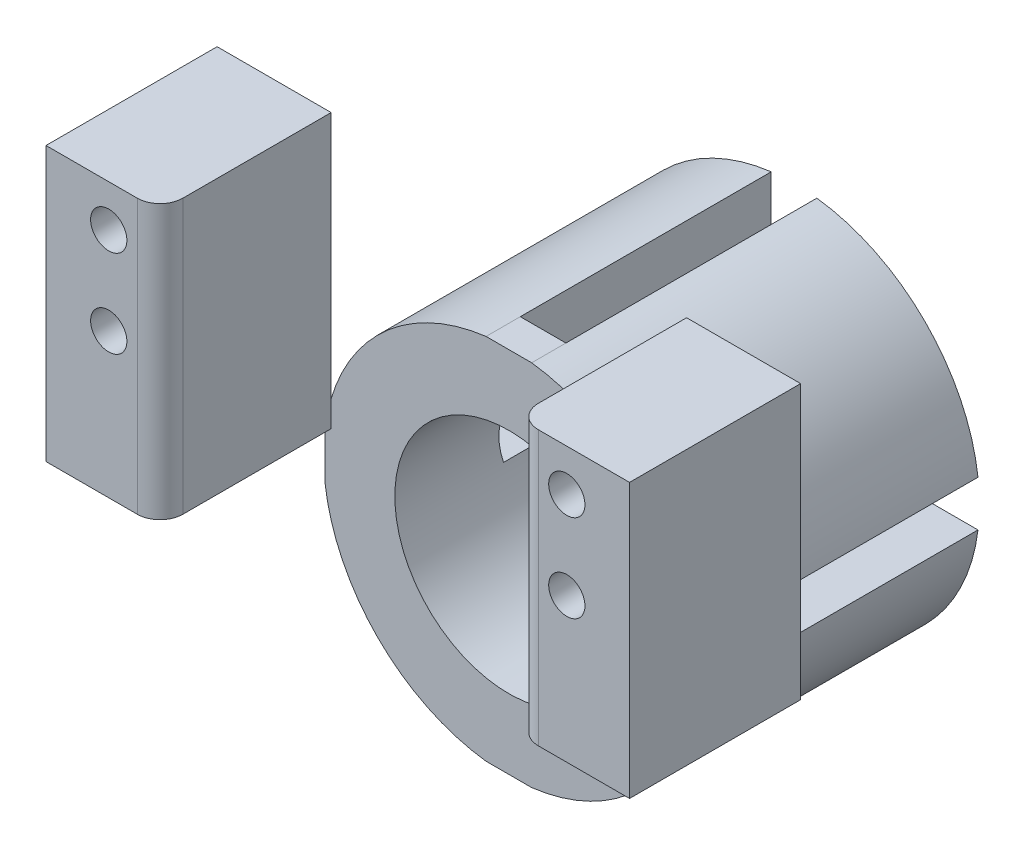
SolidWorks part; units mm, degrees
ref_plane "Front Plane" through (0, 0, 0) normal (0, 0, 1) x (1, 0, 0)
ref_plane "Top Plane" through (0, 0, 0) normal (0, 1, 0) x (1, 0, 0)
ref_plane "Right Plane" through (0, 0, 0) normal (1, 0, 0) x (0, 0, -1)
sketch "Sketch2" plane through (0, 0, 0) normal (0, 0, 1) x (1, 0, 0)
  circle A0 centre (0, 0) radius 38.1
  circle A1 centre (0, 0) radius 34.925
  dimension "D1" = 76.2
  dimension "D2" = 69.85
sketch "Sketch4" plane through (0, 0, 0) normal (0, 0, 1) x (1, 0, 0)
  line L0 (-16.6687, -2.54) -> (-16.6687, 2.54) construction
  line L1 (-12.7, 0) -> (-20.6375, 0) construction
  line L2 (-12.4434, 2.54) -> (-20.4806, 2.54)
  line L3 (-12.4434, -2.54) -> (-20.4806, -2.54)
  line L4 (-2.54, 12.4434) -> (-2.54, 20.4806)
  line L5 (2.54, 12.4434) -> (2.54, 20.4806)
  line L6 (12.4434, 2.54) -> (20.4806, 2.54)
  line L7 (12.4434, -2.54) -> (20.4806, -2.54)
  line L8 (2.54, -12.4434) -> (2.54, -20.4806)
  line L9 (-2.54, -12.4434) -> (-2.54, -20.4806)
  circle A1 centre (0, 0) radius 20.6375
  circle A2 centre (0, 0) radius 12.7
  point P5 (-16.6687, 0)
  point P29 (0, 0)
  dimension "D4" = 4
  dimension "D2" = 41.275
  dimension "D1" = 5.08
  dimension "D3" = 25.4
extrude "Boss-Extrude3" add sketch "Sketch4" against normal blind 31.75
sketch "Sketch6" plane through (0, 0, 0) normal (0, 0, 1) x (1, 0, 0)
  line L0 (0, 0) -> (24.8393, 24.8393) construction
  line L1 (0, 0) -> (34.925, 0) construction
  line L2 (21.3944, 28.2843) -> (28.2843, 21.3944) construction
  circle A1 centre (0, 0) radius 35.4644 construction
  circle A2 centre (0, 0) radius 34.925 construction
  point P9 (24.8393, 24.8393)
  dimension "D2" = 70.9287
  dimension "D1" = 45
  dimension "D3" = 9.7437
sketch "Sketch7" plane through (0, 2.54, 0) normal (0, -1, 0) x (1, 0, 0)
  line L0 (20.4806, -31.75) -> (20.4806, 0) construction
  line L1 (12.4434, -11.8472) -> (20.4806, -3.81)
  line L4 (20.4806, 0) -> (12.4434, 0)
  line L5 (12.4434, 0) -> (12.4434, -31.75)
  line L6 (12.4434, -31.75) -> (20.4806, -31.75)
  line L7 (20.4806, -31.75) -> (20.4806, 0)
  line L8 (20.4806, 0) -> (12.4434, 0)
  line L9 (12.4434, 0) -> (12.4434, -11.8472)
  line L13 (20.4806, -3.81) -> (20.4806, 0)
  point P2 (0, 0)
  point P3 (24.9538, 0)
  point P5 (20.4806, -3.3598)
  line M6 (20.4806, 0) -> (12.4434, 0)
  line M7 (12.4434, 0) -> (12.4434, -31.75)
  line M9 (20.4806, -31.75) -> (20.4806, 0)
  dimension "D2" = 45
  dimension "D3" = 3.81
  dimension "D1" = 0
extrude "Boss-Extrude4" add sketch "Sketch7" along normal blind 5.08 separate body contours L1 M7 M9 M6
pattern_circular "CirPattern2" count 4 over 360 about axis through (0, 0, 0) along (0, 0, 1) of bodies 108
combine bodies "Combine1" bodies to combine 107 111 106 112 105 108 104 110
sketch "Sketch8" plane through (0, 0, 0) normal (0, 0, 1) x (1, 0, 0)
  line L0 (-2.54, -12.4434) -> (2.54, -12.4434) construction
  line L1 (2.54, 12.4434) -> (-2.54, 12.4434) construction
  line L2 (-12.4434, 2.54) -> (-12.4434, -2.54) construction
  line L3 (12.4434, -2.54) -> (12.4434, 2.54) construction
  line L4 (12.4434, -2.54) -> (12.4434, 2.54)
  line L5 (2.54, 12.4434) -> (-2.54, 12.4434)
  line L6 (-12.4434, 2.54) -> (-12.4434, -2.54)
  line L7 (-2.54, -12.4434) -> (2.54, -12.4434)
  circle A0 centre (0, 0) radius 12.7
  line M1 (-12.4434, -2.54) -> (-12.4434, 2.54)
  line M3 (-2.54, 12.4434) -> (2.54, 12.4434)
  line M5 (12.4434, 2.54) -> (12.4434, -2.54)
  line M7 (2.54, -12.4434) -> (-2.54, -12.4434)
extrude "Cut-Extrude1" cut sketch "Sketch8" against normal blind 47.752 contours A0 M3 | A0 M5 | A0 M7 | A0 M1
ref_plane "Plane2" through (0, 0, 19.05) normal (0, 0, 1) x (1, 0, 0)
sketch "Sketch10" plane through (0, 0, 19.05) normal (0, 0, 1) x (1, 0, 0)
  line L0 (0, 0) -> (25.0771, 25.0771) construction
  line L1 (0, 0) -> (0, 20.6375) construction
  line L2 (21.3944, 28.2843) -> (28.2843, 21.3944) construction
  line L3 (28.2843, 21.3944) -> (-7.7782, -14.668) construction
  line L4 (-7.7782, -14.668) -> (-14.668, -7.7782) construction
  line L5 (-14.668, -7.7782) -> (21.3944, 28.2843) construction
  line L10 (27.5334, 14.063) -> (35.6156, 22.1453)
  line L11 (35.6156, 22.1453) -> (22.1453, 35.6156)
  line L12 (22.1453, 35.6156) -> (14.063, 27.5334)
  line L13 (14.063, 27.5334) -> (27.5334, 14.063)
  line L14 (10.253, 3.3632) -> (3.3632, 10.253) construction
  line L15 (-21.9994, -8.529) -> (-13.9172, -0.4468)
  line L16 (-8.529, -21.9994) -> (-21.9994, -8.529)
  line L17 (-0.4468, -13.9172) -> (-8.529, -21.9994)
  line L18 (-13.9172, -0.4468) -> (-0.4468, -13.9172)
  arc A0 (29.4561, 19.7499) -> (19.7499, 29.4561) centre (0, 0) ccw construction
  circle A1 centre (28.2843, 21.3944) radius 2.0193
  circle A2 centre (21.3944, 28.2843) radius 2.0193
  circle A3 centre (-7.7782, -14.668) radius 2.0193
  circle A4 centre (-14.668, -7.7782) radius 2.0193
  arc A5 (20.4806, 2.54) -> (2.54, 20.4806) centre (0, 0) ccw construction
  circle A6 centre (0, 0) radius 12.7 construction
  circle A7 centre (0, 0) radius 12.7 construction
  point P10 (24.8393, 24.8393)
  point P15 (24.8393, 24.8393)
  point P22 (20.7982, 20.7982)
  dimension "D1" = 70.9287
  dimension "D5" = 4.0386
  dimension "D2" = 45
  dimension "D3" = 9.7437
  dimension "D4" = 51
  dimension "D6" = 5.715
  dimension "D7" = 11.43
  dimension "D8" = 19.05
extrude "Boss-Extrude5" [suppressed] add sketch "Sketch10" against normal up to surface (12.7 mm away) contours L12 L13 L10 L11 A2 A1 | A1 | A2 | L15 A7 L17 L18 A4 A3 | A7 L15 L16 L17 | A3 | A4
sketch "Sketch11" plane through (0, 0, 0) normal (0, 0, 1) x (1, 0, 0)
  line L0 (19.785, 14.3968) -> (32.485, 14.3968) construction
  line L1 (-25.5, 19.05) -> (25.5, 19.05) construction
  line L2 (-25.5, 19.05) -> (-25.5, 28.7937) construction
  line L3 (-25.5, 28.7937) -> (25.5, 28.7937) construction
  line L4 (25.5, 19.05) -> (25.5, 28.7937) construction
  line L5 (0, 0) -> (0, 20.6375) construction
  line L6 (0, 19.05) -> (0, 28.7937) construction
  line L7 (-19.785, 33.4468) -> (-32.485, 33.4468)
  line L8 (-19.785, 33.4468) -> (-19.785, 14.3968) construction
  line L9 (-19.785, 14.3968) -> (-32.485, 14.3968) construction
  line L10 (-32.485, 33.4468) -> (-32.485, 14.3968)
  line L11 (32.485, 33.4468) -> (32.485, 14.3968)
  line L12 (19.785, 33.4468) -> (19.785, 14.3968) construction
  line L13 (19.785, 33.4468) -> (32.485, 33.4468)
  line L14 (-32.485, 14.3968) -> (-32.485, 2.9668)
  line L15 (-32.485, 2.9668) -> (-19.785, 2.9668)
  line L16 (-19.785, 2.9668) -> (-19.785, 33.4468)
  line L18 (32.485, 2.9668) -> (19.785, 2.9668)
  line L19 (19.785, 2.9668) -> (19.785, 33.4468)
  line L21 (32.485, 14.3968) -> (32.485, 2.9668)
  circle A1 centre (-25.5, 19.05) radius 2.0193 construction
  circle A2 centre (-25.5, 28.7937) radius 2.0193 construction
  circle A3 centre (25.5, 28.7937) radius 2.0193 construction
  circle A4 centre (25.5, 19.05) radius 2.0193 construction
  circle A5 centre (0, 0) radius 12.7 construction
  point P5 (0, 19.05)
  point P14 (-25.5, 23.9218)
  point P19 (-32.485, 23.9218)
  dimension "D3" = 4.0386
  dimension "D7" = 19.05
  dimension "D1" = 9.7437
  dimension "D2" = 51
  dimension "D4" = 19.05
  dimension "D5" = 12.7
  dimension "D6" = 5.715
  dimension "D8" = 11.43
extrude "Boss-Extrude6" add sketch "Sketch11" along normal up to surface (19.05 mm away) up to plane "Plane2"
sketch "Sketch12" plane through (0, 0, 19.05) normal (0, 0, 1) x (1, 0, 0)
  circle A0 centre (25.5, 28.7937) radius 2.0193 construction
  circle A1 centre (25.5, 19.05) radius 2.0193 construction
  circle A2 centre (-25.5, 28.7937) radius 2.0193 construction
  circle A3 centre (-25.5, 19.05) radius 2.0193 construction
  circle A4 centre (25.5, 28.7937) radius 2.0193
  circle A5 centre (25.5, 19.05) radius 2.0193
  circle A6 centre (-25.5, 28.7937) radius 2.0193
  circle A7 centre (-25.5, 19.05) radius 2.0193
extrude "Cut-Extrude2" cut sketch "Sketch12" against normal blind 5.461
fillet "Fillet5" radius 2.54 2 edges at (-19.785, 18.2068, 19.05) (19.785, 18.2068, 19.05)
